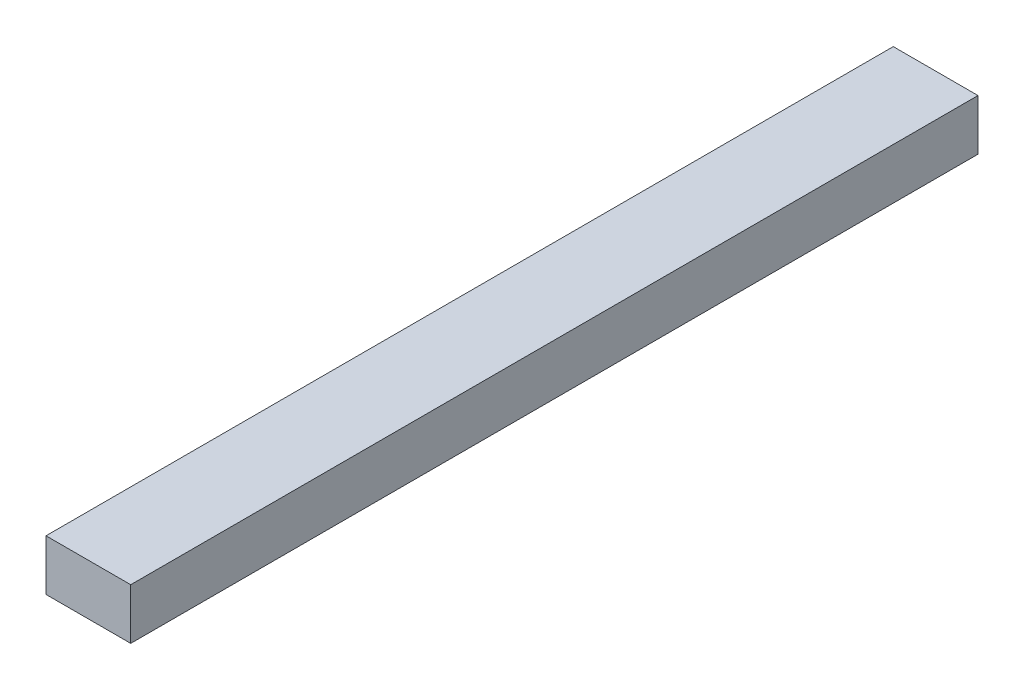
SolidWorks part; units mm, degrees
ref_plane "Front Plane" through (0, 0, 0) normal (0, 0, 1) x (1, 0, 0)
ref_plane "Top Plane" through (0, 0, 0) normal (0, 1, 0) x (1, 0, 0)
ref_plane "Right Plane" through (0, 0, 0) normal (1, 0, 0) x (0, 0, -1)
sketch "Sketch2" plane through (0, 0, 0) normal (0, 1, 0) x (1, 0, 0)
  line L1 (-2.5, 25) -> (2.5, 25)
  line L2 (-2.5, 25) -> (-2.5, -25)
  line L3 (-2.5, -25) -> (2.5, -25)
  line L4 (2.5, 25) -> (2.5, -25)
  line L5 (-2.5, 25) -> (2.5, -25) construction
  line L6 (-2.5, -25) -> (2.5, 25) construction
  point P0 (0, 0)
  dimension "D1" = 5
  dimension "D2" = 50
extrude "Boss-Extrude1" add sketch "Sketch2" along normal blind 3
